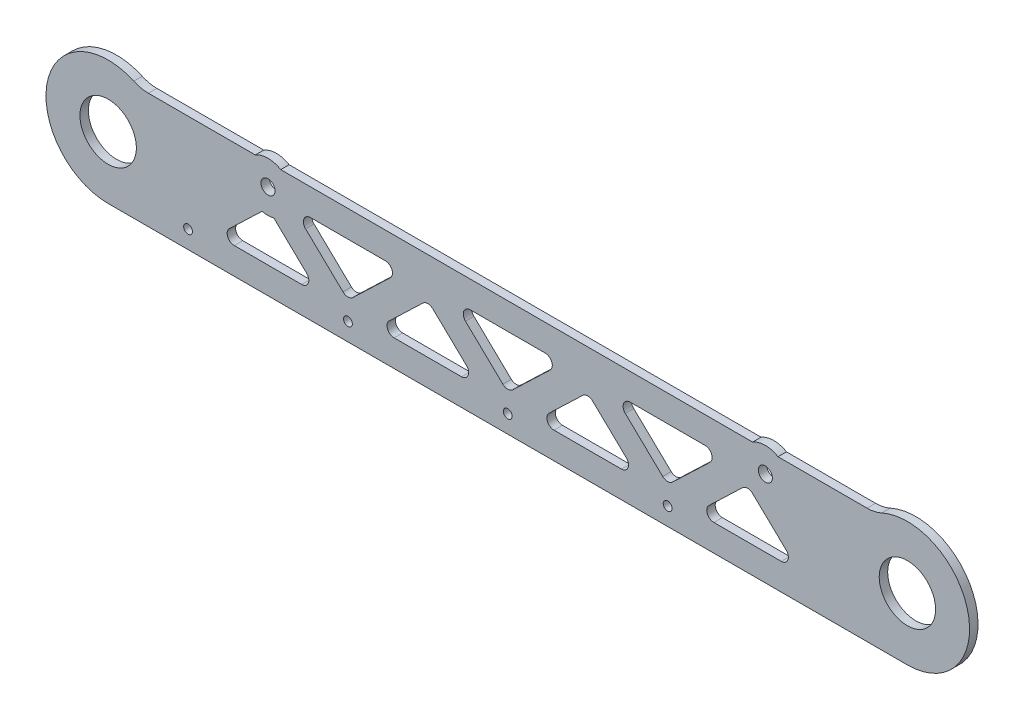
SolidWorks part; units mm, degrees
material "6061-T6 (SS)"
ref_plane "Front" through (0, 0, 0) normal (0, 0, 1) x (1, 0, 0)
ref_plane "Top" through (0, 0, 0) normal (0, 1, 0) x (1, 0, 0)
ref_plane "Right" through (0, 0, 0) normal (1, 0, 0) x (0, 0, -1)
sketch "Sketch1" plane through (0, 0, 0) normal (0, 0, 1) x (1, 0, 0)
  line L0 (-225, 35) -> (225, 35)
  line L1 (-225, -35) -> (225, -35)
  line L2 (-225, 0) -> (225, 0) construction
  arc A0 (-225, 35) -> (-225, -35) centre (-225, 0) ccw
  arc A1 (225, 35) -> (225, -35) centre (225, 0) cw
  point P6 (0, 0)
  dimension "D2" = 70
  dimension "D1" = 450
extrude "Boss-Extrude1" add sketch "Sketch1" along normal blind 4.7625
sketch "Sketch2" plane through (0, 0, 0) normal (0, 0, -1) x (-1, 0, 0)
  circle A0 centre (-145, 18.1) radius 3.9687
  circle A1 centre (135, 18.1) radius 3.9687
  arc A2 (225, -35) -> (225, 35) centre (225, 0) ccw construction
  arc A3 (-225, 35) -> (-225, -35) centre (-225, 0) ccw construction
  circle A4 centre (-225, 0) radius 15.875
  circle A5 centre (225, 0) radius 15.875
  dimension "D5" = 7.9375
  dimension "D6" = 7.9375
  dimension "D7" = 31.75
  dimension "D1" = 18.1
  dimension "D2" = 18.1
  dimension "D3" = 90
  dimension "D4" = 80
extrude "Cut-Extrude1" cut sketch "Sketch2" against normal through all both and the other way through all
hole_wizard "#10 Clearance Hole1" [suppressed] positions "Sketch5" profile "Sketch6" hole size "#10" standard "ANSI Inch"
sketch "Sketch5" plane through (0, 0, 4.7625) normal (0, 0, 1) x (1, 0, 0)
  line L1 (225, 38.1) -> (-225, 38.1) construction
  line L2 (-225, -38.1) -> (225, -38.1) construction
  point P0 (-170, 28.1)
  point P2 (-132.5, -28.1)
  point P29 (-80, 28.1)
  point P30 (10, 28.1)
  point P31 (100, 28.1)
  point P38 (-42.5, -28.1)
  point P39 (47.5, -28.1)
  point P40 (137.5, -28.1)
  dimension "D1" = 4
  dimension "D2" = 4
  dimension "D3" = 10
  dimension "D4" = 10
  dimension "D5" = 90
  dimension "D6" = 90
  dimension "D7" = 55
  dimension "D8" = 92.5
sketch "Sketch6" plane through (-170, 28.1, 4.7625) normal (1, 0, 0) x (0, -1, 0)
  line L0 (0, 0) -> (0, 4.7625)
  line L1 (0, 4.7625) -> (2.4892, 4.7625)
  line L2 (2.4892, 4.7625) -> (2.4892, 0)
  line L5 (2.4892, 0) -> (0, 0)
  line L11 (0, -6.35) -> (0, 107.95) construction
  dimension "Thru Hole Dia." = 4.9784
  dimension "Thru Hole Depth" = 4.7625
hole_wizard "#10 Clearance Hole2" positions "Sketch7" profile "Sketch8" hole size "#10" standard "ANSI Inch" end condition through all
sketch "Sketch7" plane through (0, 0, 4.7625) normal (0, 0, 1) x (1, 0, 0)
  line L0 (-225, -35) -> (225, -35) construction
  arc A0 (-225, 35) -> (-225, -35) centre (-225, 0) ccw construction
  point P0 (-180, -25)
  point P8 (-90, -25)
  point P9 (0, -25)
  point P10 (90, -25)
  dimension "D2" = 90
  dimension "D3" = 10
  dimension "D4" = 45
  dimension "D1" = 4
sketch "Sketch8" plane through (-180, -25, 4.7625) normal (1, 0, 0) x (0, -1, 0)
  line L0 (0, 0) -> (0, 4.7625)
  line L1 (0, 4.7625) -> (2.4892, 4.7625)
  line L2 (2.4892, 4.7625) -> (2.4892, 0)
  line L5 (2.4892, 0) -> (0, 0)
  line L11 (0, -6.35) -> (0, 107.95) construction
  dimension "Thru Hole Dia." = 4.9784
  dimension "Thru Hole Depth" = 4.7625
sketch "Sketch16" plane through (0, 0, 4.7625) normal (0, 0, 1) x (1, 0, 0)
  line L0 (-207.1397, 30.1) -> (207.1397, 30.1)
  line L1 (-225, 35) -> (225, 35)
  arc A1 (-225, 35) -> (-207.1397, 30.1) centre (-225, 0) cw
  arc A2 (225, 35) -> (207.1397, 30.1) centre (225, 0) ccw
  circle A3 centre (-135, 18.1) radius 3.9687 construction
  dimension "D1" = 12
extrude "Cut-Extrude3" cut sketch "Sketch16" against normal through all
sketch "Sketch17" plane through (0, 0, 4.7625) normal (0, 0, 1) x (1, 0, 0)
  line L6 (-135, 18.1) -> (-190.4408, -35) construction
  line L7 (-225, -35) -> (225, -35) construction
  line L8 (-190.4408, -35) -> (-79.5592, -35) construction
  line L9 (-79.5592, -35) -> (-135, 18.1) construction
  line L10 (-135, 7.7149) -> (-171.7673, -27.5)
  line L11 (-171.7673, -27.5) -> (-98.2327, -27.5)
  line L12 (-98.2327, -27.5) -> (-135, 7.7149)
  line L13 (-163.9367, -20) -> (-106.0633, -20)
  circle A0 centre (-90, -25) radius 2.4892 construction
  circle A1 centre (-180, -25) radius 2.4892 construction
  circle A2 centre (-90, -25) radius 2.4892 construction
  circle A3 centre (-180, -25) radius 2.4892 construction
  dimension "D2" = 7.5
  dimension "D1" = 7.5
extrude "Cut-Extrude4" cut sketch "Sketch17" against normal through all contours L10 L13 L12
fillet "Fillet1" radius 4 3 edges at (-135, 7.7149, 2.3813) (-106.0633, -20, 2.3813) (-163.9367, -20, 2.3813)
pattern_linear "LPattern1" count 4 spacing 90 along (1, 0, 0) of "Cut-Extrude4", "Fillet1"
sketch "Sketch18" plane through (0, 0, 4.7625) normal (0, 0, 1) x (1, 0, 0)
  line L3 (-147.529, 30.1) -> (-90, -25) construction
  line L4 (-207.1397, 30.1) -> (207.1397, 30.1) construction
  line L5 (-90, -25) -> (-32.471, 30.1) construction
  line L6 (-32.471, 30.1) -> (-147.529, 30.1) construction
  line L7 (-51.1445, 22.6) -> (-128.8555, 22.6)
  line L8 (-128.8555, 22.6) -> (-90, -14.6149)
  line L9 (-90, -14.6149) -> (-51.1445, 22.6)
  line L10 (-121.0248, 15.1) -> (-58.9752, 15.1)
  circle A0 centre (-135, 18.1) radius 3.9687 construction
  circle A1 centre (-135, 18.1) radius 3.9687 construction
  dimension "D2" = 7.5
  dimension "D1" = 7.5
extrude "Cut-Extrude5" cut sketch "Sketch18" against normal through all contours L10 L8 L9
fillet "Fillet2" radius 4 3 edges at (-90, -14.6149, 2.3813) (-58.9752, 15.1, 2.3813) (-121.0248, 15.1, 2.3813)
pattern_linear "LPattern2" count 3 spacing 90 along (1, 0, 0) of "Fillet2", "Cut-Extrude5"
sketch "Sketch13" plane through (0, 0, 4.7625) normal (0, 0, 1) x (1, 0, 0)
  circle A0 centre (-135, 18.1) radius 13.9687
  circle A1 centre (145, 18.1) radius 3.9687 construction
  circle A2 centre (-135, 18.1) radius 3.9687 construction
  circle A3 centre (145, 18.1) radius 3.9687
  circle A4 centre (-135, 18.1) radius 3.9687
  circle A5 centre (145, 18.1) radius 13.9687
  dimension "D1" = 10
extrude "Boss-Extrude2" add sketch "Sketch13" against normal up to surface (4.7625 mm away) up to face at (90, 3.9086, 0)
fillet "Fillet3" radius 20 2 edges at (207.1397, 30.1, 2.3813) (-207.1397, 30.1, 2.3813)
sketch "Sketch14" plane through (0, 0, 4.7625) normal (0, 0, 1) x (1, 0, 0)
  line L0 (-115, -10) -> (152.0293, -10) construction
  line L1 (-225, -35) -> (225, -35) construction
  circle A0 centre (-225, 0) radius 15.875 construction
  text T0 "uORover" font "Impact" height 50
  dimension "D1" = 25
  dimension "D2" = 110
extrude "Cut-Extrude2" [suppressed] cut sketch "Sketch14" against normal through all
sketch "Sketch9" [suppressed] plane through (0, 0, 4.7625) normal (0, 0, 1) x (1, 0, 0)
  line L0 (-138.5969, 5.875) -> (-167.1753, -23.7217)
  line L1 (-163.5784, -32.1948) -> (-106.4216, -32.1948)
  line L2 (-102.8247, -23.7217) -> (-131.4031, 5.875)
  line L3 (-93.8303, 9.5645) -> (-53.5355, -30.7303)
  line L4 (-46.4645, -30.7303) -> (-6.1697, 9.5645)
  line L5 (-9.7052, 18.1) -> (-90.2948, 18.1)
  line L12 (-90, -34.05) -> (-152.8861, -8.9234) construction
  line L13 (-180, -34.05) -> (-117.1139, -8.9234) construction
  line L14 (-50, 18.1) -> (-50, -34.05) construction
  line L15 (-90, -34.05) -> (0, -34.05) construction
  line L16 (90.2948, 18.1) -> (9.7052, 18.1)
  line L17 (6.1697, 9.5645) -> (46.4645, -30.7303)
  line L18 (53.5355, -30.7303) -> (93.8303, 9.5645)
  line L22 (0, -34.05) -> (90, -34.05) construction
  line L23 (50, 18.1) -> (50, -34.05) construction
  line L24 (172.1753, -23.7217) -> (143.5969, 5.875)
  line L25 (136.4031, 5.875) -> (107.8247, -23.7217)
  line L26 (111.4216, -32.1948) -> (168.5784, -32.1948)
  arc A0 (-6.1697, 9.5645) -> (-9.7052, 18.1) centre (-9.7052, 13.1) ccw
  circle A1 centre (-90, -34.05) radius 2.4892 construction
  circle A2 centre (-180, -34.05) radius 2.4892 construction
  arc A3 (-93.8303, 9.5645) -> (-90.2948, 18.1) centre (-90.2948, 13.1) cw
  arc A4 (-53.5355, -30.7303) -> (-46.4645, -30.7303) centre (-50, -27.1948) ccw
  arc A5 (-106.4216, -32.1948) -> (-102.8247, -23.7217) centre (-106.4216, -27.1948) ccw
  arc A6 (-167.1753, -23.7217) -> (-163.5784, -32.1948) centre (-163.5784, -27.1948) ccw
  arc A7 (-138.5969, 5.875) -> (-131.4031, 5.875) centre (-135, 2.4019) cw
  arc A8 (6.1697, 9.5645) -> (9.7052, 18.1) centre (9.7052, 13.1) cw
  arc A9 (93.8303, 9.5645) -> (90.2948, 18.1) centre (90.2948, 13.1) ccw
  arc A10 (46.4645, -30.7303) -> (53.5355, -30.7303) centre (50, -27.1948) ccw
  arc A11 (136.4031, 5.875) -> (143.5969, 5.875) centre (140, 2.4019) cw
  arc A12 (168.5784, -32.1948) -> (172.1753, -23.7217) centre (168.5784, -27.1948) ccw
  arc A13 (107.8247, -23.7217) -> (111.4216, -32.1948) centre (111.4216, -27.1948) ccw
  point P6 (-135, 18.1)
  point P16 (2.3659, 18.1)
  point P29 (-102.3659, 18.1)
  point P35 (-94.6431, -32.1948)
  point P38 (-175.3569, -32.1948)
  point P41 (-135, 9.6)
  dimension "D4" = 5
  dimension "D1" = 8.5
  dimension "D2" = 5
  dimension "D3" = 5
  dimension "D7" = 50
  dimension "D8" = 50
  dimension "D9" = 275
  dimension "D6" = 2
  dimension "D5" = 2
